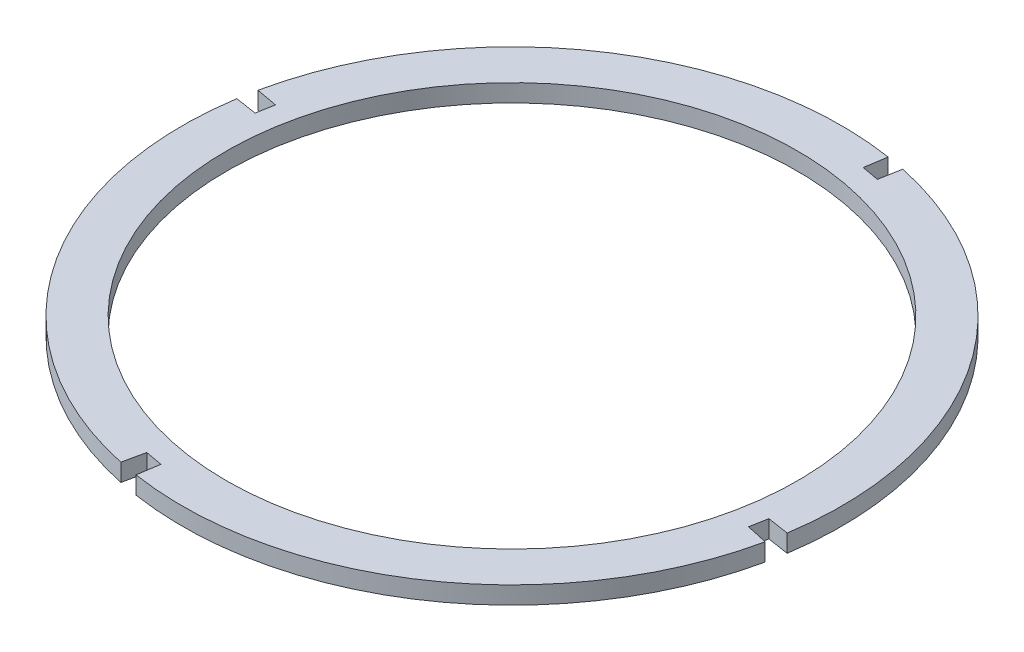
SolidWorks part; units mm, degrees
ref_plane "Спереди" through (0, 0, 0) normal (0, 0, 1) x (1, 0, 0)
ref_plane "Сверху" through (0, 0, 0) normal (0, 1, 0) x (1, 0, 0)
ref_plane "Справа" through (0, 0, 0) normal (1, 0, 0) x (0, 0, -1)
other "Configuration Table"
sketch "Эскиз1" plane through (0, 0, 0) normal (0, 1, 0) x (1, 0, 0)
  line L0 (-564.1311, 487.3983) -> (-548.3966, 484.4957)
  line L1 (-607.0603, 210.5932) -> (-556.2639, 485.947) construction
  line L3 (-564.1311, 487.3983) -> (-561.0835, 507.0491)
  line L4 (-548.3966, 484.4957) -> (-544.7876, 504.0589)
  line L6 (-556.2639, 485.947) -> (-657.6975, -64.79) construction
  line L7 (-607.0603, 210.5932) -> (-331.7065, 159.7968) construction
  line L8 (-607.0603, 210.5932) -> (-882.4141, 261.3896) construction
  line L9 (-330.2552, 167.664) -> (-333.1578, 151.9295)
  line L10 (-333.1578, 151.9295) -> (-313.7131, 147.7649)
  line L11 (-330.2552, 167.664) -> (-310.6043, 164.6164)
  line L12 (-665.5652, -63.3409) -> (-649.8299, -66.239)
  line L13 (-665.5652, -63.3409) -> (-669.7191, -82.7903)
  line L14 (-649.8299, -66.239) -> (-652.8658, -85.8893)
  line L15 (-880.9628, 269.2569) -> (-883.8654, 253.5224)
  line L16 (-880.9628, 269.2569) -> (-900.526, 272.8658)
  line L17 (-883.8654, 253.5224) -> (-903.5163, 256.57)
  arc A0 (-561.0835, 507.0491) -> (-900.526, 272.8658) centre (-607.0603, 210.5932) ccw
  circle A1 centre (-607.0603, 210.5932) radius 260
  arc A2 (-310.6043, 164.6164) -> (-544.7876, 504.0589) centre (-607.0603, 210.5932) ccw
  arc A3 (-652.8658, -85.8893) -> (-313.7131, 147.7649) centre (-607.0603, 210.5932) ccw
  arc A4 (-903.5163, 256.57) -> (-669.7191, -82.7903) centre (-607.0603, 210.5932) ccw
  point P7 (-556.2639, 485.947)
  point P13 (-657.6975, -64.79)
  point P16 (-331.7065, 159.7968)
  point P24 (-882.4141, 261.3896)
  dimension "D1" = 600
  dimension "D2" = 520
  dimension "D3" = 0
  dimension "D4" = 0
  dimension "D5" = 16
  dimension "D6" = 16
  dimension "D7" = 0
  dimension "D8" = 280
  dimension "D9" = 16
  dimension "D10" = 0
  dimension "D11" = 16
  dimension "D12" = 0
  dimension "D13" = 280
  dimension "D14" = 280
  dimension "D15" = 280
  dimension "D16" = 0
extrude "Бобышка-Вытянуть3" add sketch "Эскиз1" along normal blind 16
